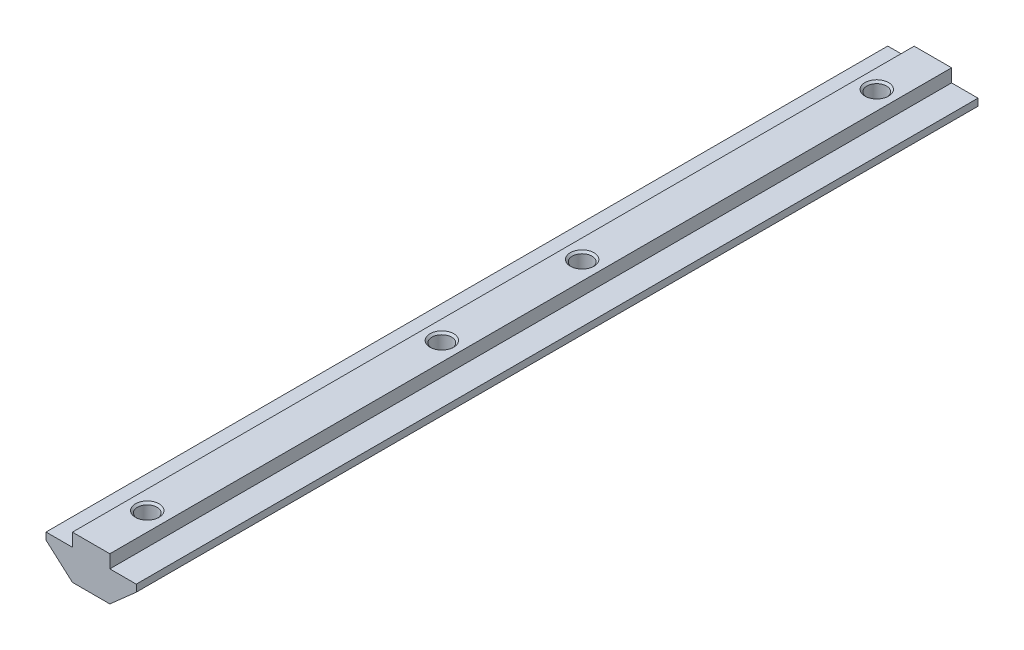
SolidWorks part; units mm, degrees
ref_plane "Спереди" through (0, 0, 0) normal (0, 0, 1) x (1, 0, 0)
ref_plane "Сверху" through (0, 0, 0) normal (0, 1, 0) x (1, 0, 0)
ref_plane "Справа" through (0, 0, 0) normal (1, 0, 0) x (0, 0, -1)
sketch "Эскиз1" plane through (0, 0, 0) normal (0, 0, 1) x (1, 0, 0)
  line L0 (4, 0) -> (-4, 0)
  line L1 (-4, 0) -> (-4, -2.8)
  line L2 (-4, -2.8) -> (-9.65, -2.8)
  line L3 (-9.65, -2.8) -> (-9.65, -4.3)
  line L4 (-9.65, -4.3) -> (-4, -9.3)
  line L5 (-4, -9.3) -> (4, -9.3)
  line L6 (0, -9.3) -> (0, 0) construction
  line L7 (9.65, -4.3) -> (4, -9.3)
  line L8 (9.65, -2.8) -> (9.65, -4.3)
  line L9 (4, -2.8) -> (9.65, -2.8)
  line L10 (4, 0) -> (4, -2.8)
  dimension "D1" = 8
  dimension "D2" = 19.3
  dimension "D3" = 9.3
  dimension "D4" = 6.5
  dimension "D5" = 1.5
extrude "Бобышка-Вытянуть1" add sketch "Эскиз1" along normal mid plane 180
hole_wizard "Отверстие обработанное метчиком M52" positions "Эскиз5" profile "Эскиз6" tap size "M5" standard "ISO" end condition through all
sketch "Эскиз5" plane through (0, 0, 0) normal (0, 1, 0) x (1, 0, 0)
  line L0 (0, 90) -> (0, 78)
  line L1 (4, 90) -> (-4, 90) construction
  line L2 (0, 78) -> (0, 15)
  line L4 (0, -90) -> (0, -78)
  line L5 (4, -90) -> (-4, -90) construction
  line L6 (0, -78) -> (0, -15)
  point P0 (0, 78)
  point P2 (0, 15)
  point P4 (0, -15)
  point P6 (0, -78)
  dimension "D1" = 156
  dimension "D2" = 30
sketch "Эскиз6" plane through (0, 0, -78) normal (1, 0, 0) x (0, 0, 1)
  line L0 (0, 0) -> (0, 9.3)
  line L1 (0, 9.3) -> (2.525, 9.3)
  line L2 (2.1, 8.875) -> (2.1, 0.425)
  line L3 (2.1, 0.425) -> (2.525, 0)
  line L5 (2.525, 0) -> (0, 0)
  line L6 (-2.1, 0.425) -> (-2.525, 0) construction
  line L7 (2.525, 9.3) -> (2.1, 8.875)
  line L8 (-2.525, 9.3) -> (-2.1, 8.875) construction
  line L11 (0, -6.35) -> (0, 107.95) construction
  dimension "Диаметр проходного сверла" = 4.2
  dimension "Глубина проходного сверла" = 9.3
  dimension "Диаметр передней зенковки" = 5.05
  dimension "Угол передней зенковки" = 90
  dimension "Диаметр задней зенковки" = 5.05
  dimension "Угол задней зенковки" = 90
cosmetic thread "Отверстие резьбы5" parameters "D2"=5
cosmetic thread "Отверстие резьбы6" parameters "D2"=5
cosmetic thread "Отверстие резьбы7" parameters "D2"=5
cosmetic thread "Отверстие резьбы8" parameters "D2"=5
